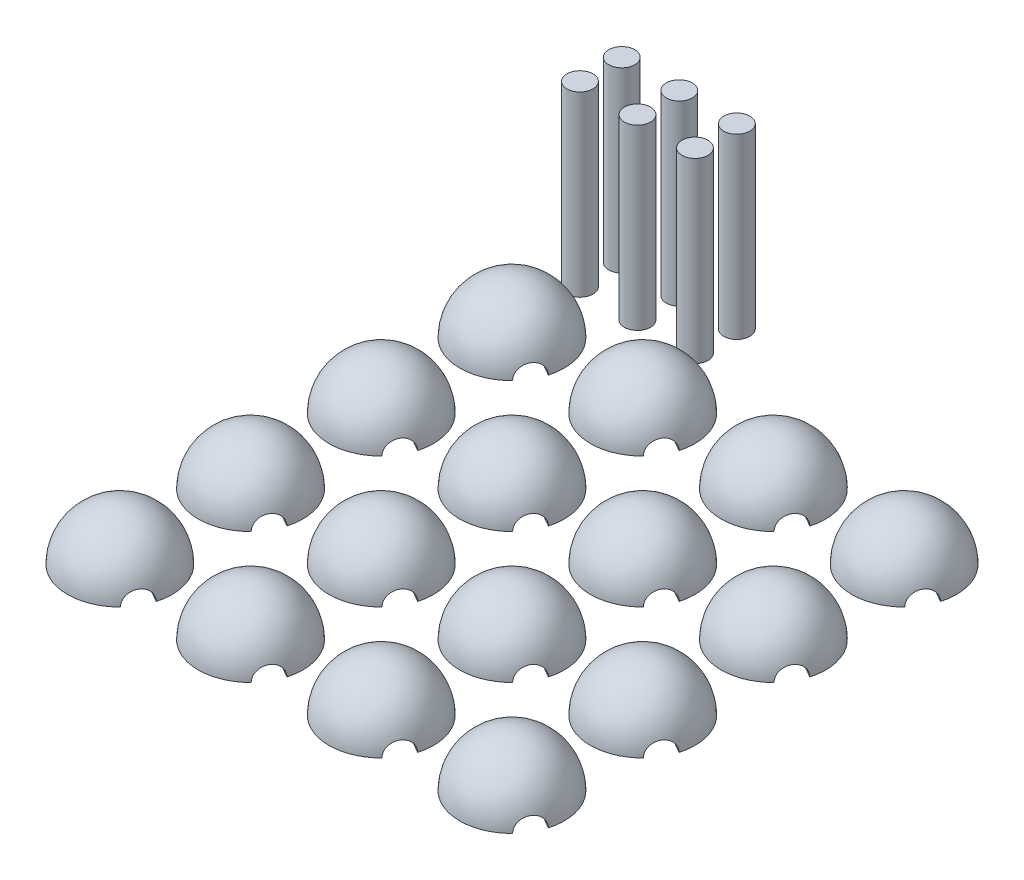
SolidWorks part; units mm, degrees
ref_plane "Front Plane" through (0, 0, 0) normal (0, 0, 1) x (1, 0, 0)
ref_plane "Top Plane" through (0, 0, 0) normal (0, 1, 0) x (1, 0, 0)
ref_plane "Right Plane" through (0, 0, 0) normal (1, 0, 0) x (0, 0, -1)
sketch "Sketch1" plane through (0, 0, 0) normal (0, 1, 0) x (1, 0, 0)
  line L0 (0, 10) -> (0, -10)
  arc A2 (0, 10) -> (0, -10) centre (0, 0) ccw
  dimension "D1" = 20
revolve "Revolve1" add sketch "Sketch1" angle 180 about L0
sketch "Sketch3" plane through (0, 0, 0) normal (0, 1, 0) x (1, 0, 0)
  line L0 (0, 0) -> (0, 10)
  line L1 (0, 0) -> (11, -6.3509)
  dimension "D1" = 120
  dimension "D2" = 11
  dimension "D3" = 10
sketch "Sketch4" plane through (0, 0, 0) normal (0, 0, 1) x (1, 0, 0)
  circle A0 centre (0, 0) radius 2.5
  dimension "D1" = 5
extrude "Cut-Extrude2" cut sketch "Sketch4" against normal blind 11 contours A0
ref_plane "Plane1" through (0, 0, 0) normal (0.866, 0, 0.5) x (0.5, 0, -0.866)
sketch "Sketch6" plane through (0, 0, 0) normal (0.866, 0, 0.5) x (0.5, 0, -0.866)
  circle A0 centre (0, 0) radius 2.5
  dimension "D1" = 5
extrude "Cut-Extrude3" cut sketch "Sketch6" along normal blind 11
sketch "Sketch10" plane through (0, 0, 0) normal (0.866, 0, 0.5) x (0.5, 0, -0.866)
  line L0 (0, 0) -> (-2.5, 0) construction
  line L1 (0, 0) -> (8.6603, 0) construction
  line L2 (-2.5, 0) -> (2.5, 0)
  arc A0 (-2.5, 0) -> (2.5, 0) centre (0, 0) cw
  dimension "D1" = 5
extrude "Boss-Extrude3" add sketch "Sketch10" along normal blind 3 contours L2 A0
sketch "Sketch11" plane through (0, 0, 0) normal (0, 0, 1) x (1, 0, 0)
  line L0 (0, 0) -> (-2.5, 0) construction
  line L1 (0, 0) -> (11, 0) construction
  line L2 (-2.5, 0) -> (2.5, 0)
  arc A0 (-2.5, 0) -> (2.5, 0) centre (0, 0) cw
  arc A1 (0, 2.5) -> (-2.5, 0) centre (0, 0) ccw construction
extrude "Boss-Extrude4" add sketch "Sketch11" against normal blind 3
sketch "Sketch12" plane through (0, 0, 0) normal (0, 1, 0) x (1, 0, 0)
  circle A0 centre (-2, 15) radius 2.495
  circle A1 centre (-2, 23) radius 2.495
  circle A2 centre (9, 23) radius 2.495
  circle A3 centre (9, 15) radius 2.495
  circle A4 centre (20, 23) radius 2.495
  circle A5 centre (20, 15) radius 2.495
  point P0 (0, 0)
  dimension "D1" = 4.99
  dimension "D3" = 4.99
  dimension "D5" = 4.99
  dimension "D6" = 4.99
  dimension "D8" = 4.99
  dimension "D9" = 4.99
  dimension "D2" = 15
  dimension "D4" = 8
  dimension "D7" = 11
  dimension "D10" = 11
  dimension "D11" = 11
  dimension "D12" = 20
  dimension "D13" = 2
extrude "Boss-Extrude5" add sketch "Sketch12" along normal blind 34 separate body
pattern_linear "LPattern18" count 4 spacing 25 along (1, 0, 0) count 4 spacing 25 along (0, 0, 1) of "Boss-Extrude4", "Boss-Extrude3", "Cut-Extrude3", "Cut-Extrude2", "Revolve1"
